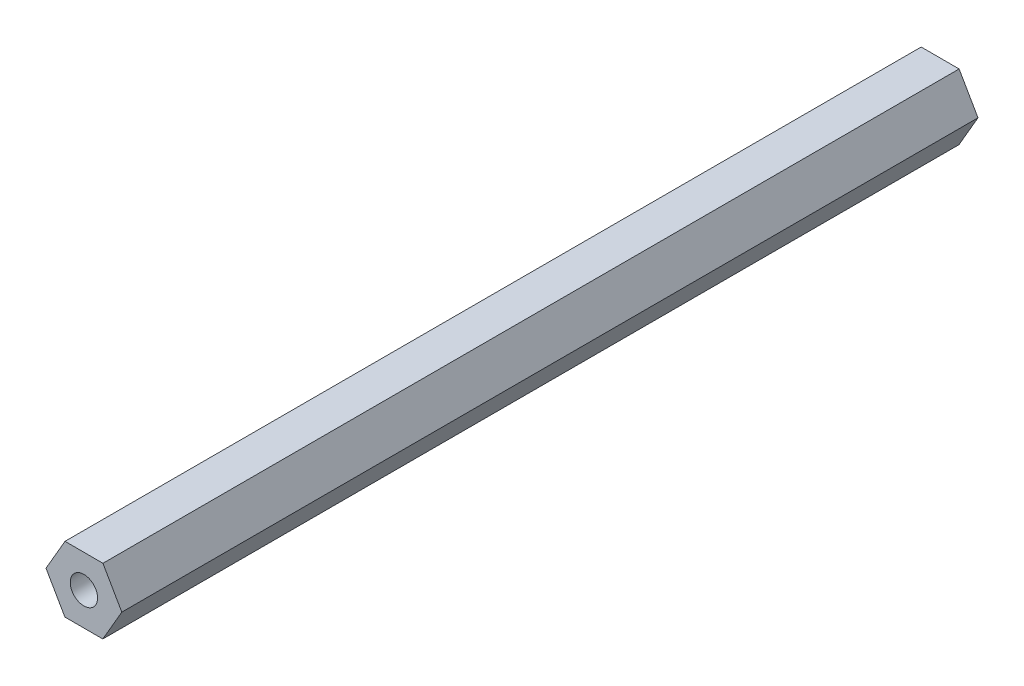
SolidWorks part; units mm, degrees
ref_plane "Front" through (0, 0, 0) normal (0, 0, 1) x (1, 0, 0)
ref_plane "Top" through (0, 0, 0) normal (0, 1, 0) x (1, 0, 0)
ref_plane "Right" through (0, 0, 0) normal (1, 0, 0) x (0, 0, -1)
sketch "Sketch1" plane through (0, 0, 0) normal (0, 0, 1) x (1, 0, 0)
  line L1 (3.4524, -6.0067) -> (6.9282, -0.0135)
  line L2 (6.9282, -0.0135) -> (3.4758, 5.9932)
  line L3 (3.4758, 5.9932) -> (-3.4524, 6.0067)
  line L4 (-3.4524, 6.0067) -> (-6.9282, 0.0135)
  line L5 (-6.9282, 0.0135) -> (-3.4758, -5.9932)
  line L6 (-3.4758, -5.9932) -> (3.4524, -6.0067)
  circle A0 centre (0, 0) radius 6 construction
  dimension "D1" = 12
extrude "Boss-Extrude1" add sketch "Sketch1" along normal blind 156.5
hole_wizard "M6x1.0 Tapped Hole1" positions "Sketch3" profile "Sketch2" tap size "M6x1.0" standard "JIS"
sketch "Sketch3" plane through (0, 0, 156.5) normal (0, 0, 1) x (1, 0, 0)
  point P0 (0, 0)
sketch "Sketch2" plane through (0, 0, 156.5) normal (1, 0, 0) x (0, -1, 0)
  line L0 (0, 0) -> (0, 18.5022)
  line L1 (0, 18.5022) -> (2.5, 17)
  line L2 (2.5, 17) -> (2.5, 0)
  line L5 (2.5, 0) -> (0, 0)
  line L10 (0, 18.5022) -> (-2.5, 17) construction
  line L11 (0, -6.35) -> (0, 107.95) construction
  dimension "ねじ下穴ﾄﾞﾘﾙ直径" = 5
  dimension "ねじ下穴ﾄﾞﾘﾙの深さ" = 17
  dimension "ﾄﾞﾘﾙ角度" = 118
cosmetic thread "Hole Thread1" parameters "D1"=12, "D2"=6
hole_wizard "M6x1.0 Tapped Hole2" positions "Sketch5" profile "Sketch4" tap size "M6x1.0" standard "JIS"
sketch "Sketch5" plane through (0, 0, 0) normal (0, 0, -1) x (-1, 0, 0)
  point P0 (0, 0)
sketch "Sketch4" plane through (0, 0, 0) normal (1, 0, 0) x (0, 1, 0)
  line L0 (0, 0) -> (0, 18.5022)
  line L1 (0, 18.5022) -> (2.5, 17)
  line L2 (2.5, 17) -> (2.5, 0)
  line L5 (2.5, 0) -> (0, 0)
  line L10 (0, 18.5022) -> (-2.5, 17) construction
  line L11 (0, -6.35) -> (0, 107.95) construction
  dimension "ねじ下穴ﾄﾞﾘﾙ直径" = 5
  dimension "ねじ下穴ﾄﾞﾘﾙの深さ" = 17
  dimension "ﾄﾞﾘﾙ角度" = 118
cosmetic thread "Hole Thread2" parameters "D1"=12, "D2"=6
